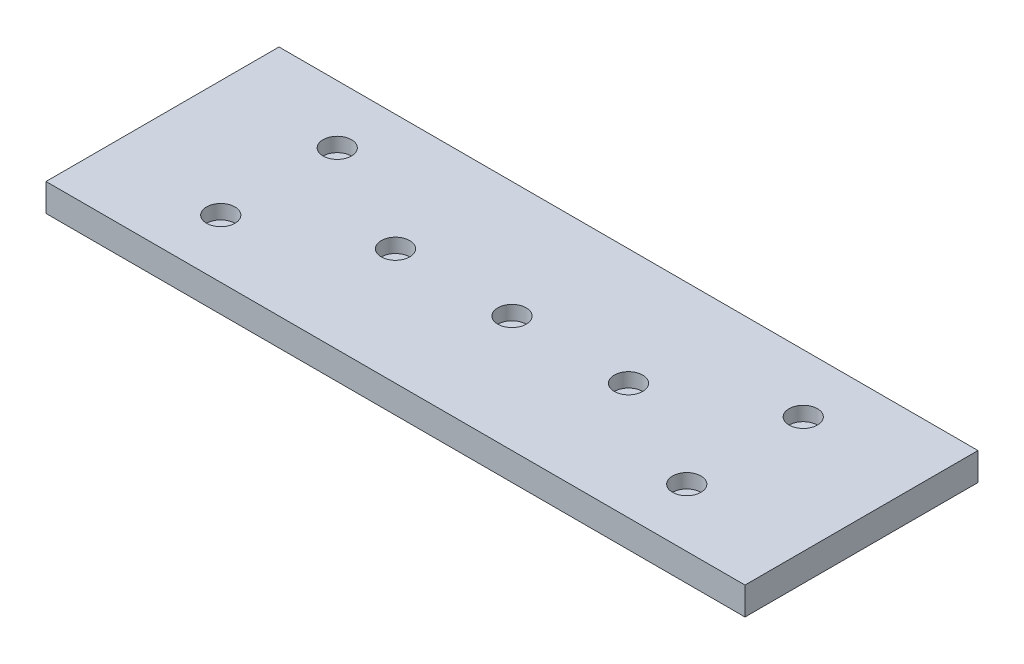
SolidWorks part; units mm, degrees
ref_plane "Front Plane" through (0, 0, 0) normal (0, 0, 1) x (1, 0, 0)
ref_plane "Top Plane" through (0, 0, 0) normal (0, 1, 0) x (1, 0, 0)
ref_plane "Right Plane" through (0, 0, 0) normal (1, 0, 0) x (0, 0, -1)
sketch "Sketch1" plane through (0, 0, 0) normal (0, 1, 0) x (1, 0, 0)
  line L1 (0, 0) -> (-150, 0)
  line L2 (0, 0) -> (0, 50)
  line L3 (0, 50) -> (-150, 50)
  line L4 (-150, 0) -> (-150, 50)
  dimension "D1" = 50
  dimension "D2" = 150
extrude "Boss-Extrude1" add sketch "Sketch1" along normal blind 5.95
sketch "Sketch2" plane through (0, 5.95, 0) normal (0, 1, 0) x (1, 0, 0)
  line L0 (-150, 25) -> (0, 25)
  line L1 (-150, 0) -> (0, 0)
  line L2 (-150, 0) -> (-150, 50)
  line L3 (-150, 50) -> (0, 50)
  line L4 (0, 0) -> (0, 50)
  line L5 (-150, 0) -> (-125, 0)
  line L6 (-125, 0) -> (-100, 0)
  line L7 (-100, 0) -> (-75, 0)
  line L8 (-75, 0) -> (-75, 25)
  line L9 (-75, 25) -> (-75, 50)
  line L10 (-75, 0) -> (-50, 0)
  line L11 (-50, 0) -> (-25, 0)
  line L12 (-25, 0) -> (0, 0)
  line L13 (-25, 0) -> (-25, 25)
  line L14 (-25, 25) -> (-25, 50)
  line L15 (-50, 0) -> (-50, 25)
  line L16 (-50, 25) -> (-50, 50)
  circle A0 centre (-25, 37.5) radius 3.05
  circle A1 centre (-25, 12.5) radius 3.05
  circle A2 centre (-50, 25) radius 3.05
  circle A3 centre (-75, 25) radius 3.05
  circle A4 centre (-100, 25) radius 3.05
  circle A5 centre (-125, 12.5) radius 3.05
  circle A6 centre (-125, 37.5) radius 3.05
extrude "Cut-Extrude1" cut sketch "Sketch2" against normal blind 3.05 contours A6 | A4 | A5 | A3 | A2 | A1 | A0
